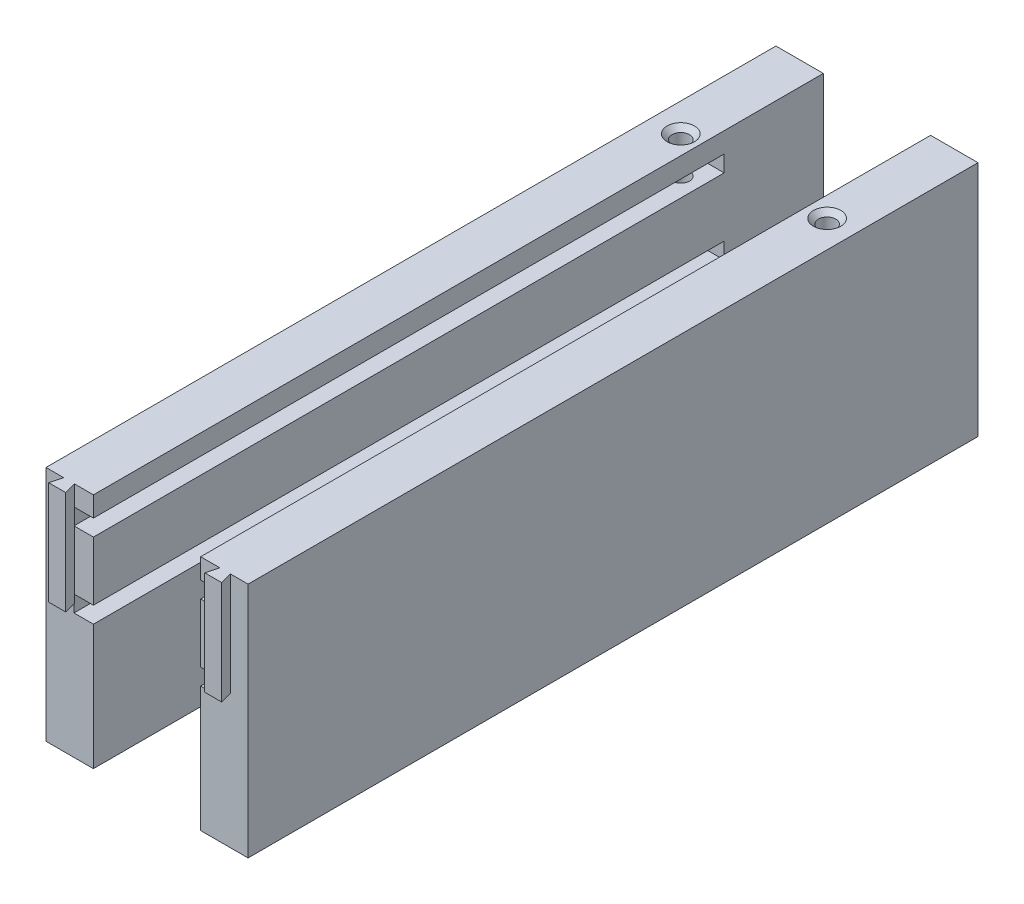
SolidWorks part; units mm, degrees
ref_plane "Front Plane" through (0, 0, 0) normal (0, 0, 1) x (1, 0, 0)
ref_plane "Top Plane" through (0, 0, 0) normal (0, 1, 0) x (1, 0, 0)
ref_plane "Right Plane" through (0, 0, 0) normal (1, 0, 0) x (0, 0, -1)
sketch "Sketch1" plane through (0, 0, 0) normal (1, 0, 0) x (0, 0, -1)
  line L1 (-64.8048, 14.1795) -> (82.1952, 14.1795)
  line L2 (-64.8048, 14.1795) -> (-64.8048, -32.8205)
  line L3 (-64.8048, -32.8205) -> (82.1952, -32.8205)
  line L4 (82.1952, 14.1795) -> (82.1952, -32.8205)
  dimension "D1" = 147
  dimension "D2" = 47
extrude "Boss-Extrude1" add sketch "Sketch1" along normal blind 8 contours L2 L3 L4 L1
sketch "Sketch12" plane through (0, 14.1795, 0) normal (0, 1, 0) x (1, 0, 0)
  line L0 (0, -62.4548) -> (2.1097, -62.4548)
  line L1 (0, -64.8048) -> (0, 82.1952) construction
  line L2 (2.1097, -62.4548) -> (1.48, -64.8048)
  line L3 (8, -64.8048) -> (0, -64.8048) construction
  line L4 (1.48, -64.8048) -> (0, -64.8048)
  line L5 (0, -64.8048) -> (0, -62.4548)
  line L6 (8, -62.4548) -> (8, -64.8048)
  line L7 (8, -64.8048) -> (8, 82.1952) construction
  line L8 (8, -64.8048) -> (4.8394, -64.8048)
  line L9 (4.8394, -64.8048) -> (4.2097, -62.4548)
  line L10 (4.2097, -62.4548) -> (8, -62.4548)
  dimension "D1" = 2.35
  dimension "D3" = 105
  dimension "D4" = 105
  dimension "D5" = 2.1
  dimension "D6" = 1.48
extrude "Cut-Extrude8" cut sketch "Sketch12" against normal blind 25
sketch "Sketch43" plane through (8, 0, 0) normal (1, 0, 0) x (0, 0, -1)
  line L0 (82.1952, -32.8205) -> (82.1952, -22.8205) construction
  line L2 (82.1952, -22.8205) -> (77.1952, -22.8205) construction
  line L3 (77.1952, -22.8205) -> (77.1952, -7.8205)
  line L4 (77.1952, -7.8205) -> (72.1952, -7.8205)
  line L5 (72.1952, -7.8205) -> (72.1952, -22.8205)
  line L6 (72.1952, -22.8205) -> (77.1952, -22.8205)
  dimension "D1" = 15
  dimension "D2" = 5
  dimension "D3" = 5
  dimension "D4" = 10
extrude "Boss-Extrude8" add sketch "Sketch43" along normal blind 6
sketch "Sketch44" plane through (8, 0, 0) normal (1, 0, 0) x (0, 0, -1)
  line L0 (82.1952, -32.8205) -> (67.1952, -32.8205) construction
  line L1 (-64.8048, -32.8205) -> (82.1952, -32.8205) construction
  line L2 (67.1952, -32.8205) -> (67.1952, -21.8205)
  line L3 (67.1952, -21.8205) -> (52.1952, -21.8205)
  line L4 (52.1952, -21.8205) -> (52.1952, -32.8205)
  line L5 (52.1952, -32.8205) -> (67.1952, -32.8205)
  dimension "D1" = 15
  dimension "D2" = 15
  dimension "D3" = 11
extrude "Boss-Extrude9" add sketch "Sketch44" along normal blind 6
sketch "Sketch13" plane through (0, -32.8205, 0) normal (0, -1, 0) x (1, 0, 0)
  line L1 (-1.916, 64.8048) -> (10.084, 64.8048)
  line L2 (-1.916, 64.8048) -> (-1.916, 62.4548)
  line L3 (-1.916, 62.4548) -> (10.084, 62.4548)
  line L4 (10.084, 64.8048) -> (10.084, 62.4548)
  line L7 (8, 64.8048) -> (0, 64.8048) construction
  dimension "D1" = 2.35
  dimension "D2" = 12
extrude "Cut-Extrude9" cut sketch "Sketch13" against normal blind 26.5
sketch "Sketch46" plane through (0, 0, 62.4548) normal (0, 0, 1) x (1, 0, 0)
  line L0 (8, 14.1795) -> (8, 10.1795) construction
  line L1 (8, -32.8205) -> (8, 14.1795) construction
  line L2 (8, 10.1795) -> (8, 6.9295)
  line L3 (8, 6.9295) -> (8, -4.7705) construction
  line L4 (8, -4.7705) -> (8, -8.0205)
  line L5 (8, 10.1795) -> (4.15, 10.1795)
  line L7 (4.15, 10.1795) -> (4.15, 6.9295)
  line L8 (4.15, 6.9295) -> (8, 6.9295)
  line L9 (8, -4.7705) -> (4.15, -4.7705)
  line L10 (4.15, -4.7705) -> (4.15, -8.0205)
  line L11 (4.15, -8.0205) -> (8, -8.0205)
  dimension "D1" = 4
  dimension "D2" = 3.25
  dimension "D3" = 11.7
  dimension "D4" = 3.25
  dimension "D5" = 3.85
  dimension "D6" = 3.85
extrude "Cut-Extrude15" cut sketch "Sketch46" against normal blind 125
ref_plane "Plane1" through (18.625, 0, 0) normal (-1, 0, 0) x (0, 0, 1)
sketch "Sketch47" plane through (0, 14.1795, 0) normal (0, 1, 0) x (1, 0, 0)
  line L0 (0, -62.4548) -> (-1.3972, -62.4548)
  line L1 (0, -62.4548) -> (0, 82.1952)
  line L2 (-1.3972, -62.4548) -> (-1.3972, 82.1952)
  line L3 (0, 82.1952) -> (-1.3972, 82.1952)
extrude "Boss-Extrude10" add sketch "Sketch47" against normal blind 47
mirror "Mirror4" about plane through (18.625, 0, 0) normal (-1, 0, 0) of bodies 140 113
hole_wizard "#8-32 Tapped Hole1" positions "Sketch35" profile "Sketch37" tap size "#8-32" standard "ANSI Inch"
sketch "Sketch35" plane through (0, 14.1795, 0) normal (0, 1, 0) x (1, 0, 0)
  point P0 (33.25, 57.6952)
  point P3 (4.25, 57.6952)
  point P4 (32.7599, 102.828)
  point P5 (33.25, 50.6952)
  point P7 (4.25, 50.6952)
sketch "Sketch37" plane through (33.25, 14.1795, -57.6952) normal (1, 0, 0) x (0, 0, 1)
  line L0 (0, 0) -> (0, 10.7074)
  line L1 (0, 10.7074) -> (1.7272, 9.6696)
  line L2 (1.7272, 9.6696) -> (1.7272, 0.9906)
  line L3 (1.7272, 0.9906) -> (2.7178, 0)
  line L5 (2.7178, 0) -> (0, 0)
  line L6 (-1.7272, 0.9906) -> (-2.7178, 0) construction
  line L10 (0, 10.7074) -> (-1.7272, 9.6696) construction
  line L11 (0, -6.35) -> (0, 107.95) construction
  dimension "Tap Drill Dia." = 3.4544
  dimension "Tap Drill Depth" = 10.7074
  dimension "Near C'Sink Dia." = 5.4356
  dimension "Near C'Sink Angle" = 90
  dimension "Drill Angle" = 118
cosmetic thread "Hole Thread2" parameters "D1"=8.33, "D2"=4.1656
cosmetic thread "Hole Thread6" parameters "D1"=8.33, "D2"=4.1656
thread "Thread3" pitch 0.7937 start angle 0, offset 1, length 10, pitch 0.7937, diameter 3.4544
ref_plane "Plane6" through (31.5228, 9.1889, -120.8538) normal (0, 0, 1) x (-1, 0, 0)
sketch "Thread Profile5" plane through (31.5228, 9.1889, -120.8538) normal (0, 0, 1) x (-1, 0, 0)
  line L0 (0, 0) -> (0, 0.7937) construction
  line L1 (0, 0) -> (0.4296, 0.248)
  line L2 (0.4296, 0.248) -> (0.4296, 0.3473)
  line L3 (0.4296, 0.3473) -> (0, 0.5953)
  line L4 (0.4296, 0.2977) -> (0, 0.2977) construction
  line L11 (0, 0) -> (0, 0.5953)
  point P2 (0, 0)
  dimension "Pitch" = 0.7937
  dimension "Profile_Angle" = 60
  dimension "Profile_Land" = 0.0992
  dimension "Profile_Height" = 0.4296
thread "Thread4" pitch 0.7937 start angle 0, offset 1, length 10, pitch 0.7937, diameter 3.4544
ref_plane "Plane7" through (2.2728, 9.1889, -120.8538) normal (0, 0, 1) x (-1, 0, 0)
sketch "Thread Profile6" plane through (2.2728, 9.1889, -120.8538) normal (0, 0, 1) x (-1, 0, 0)
  line L0 (0, 0) -> (0, 0.7937) construction
  line L1 (0, 0) -> (0.4296, 0.248)
  line L2 (0.4296, 0.248) -> (0.4296, 0.3473)
  line L3 (0.4296, 0.3473) -> (0, 0.5953)
  line L4 (0.4296, 0.2977) -> (0, 0.2977) construction
  line L11 (0, 0) -> (0, 0.5953)
  point P2 (0, 0)
  dimension "Pitch" = 0.7937
  dimension "Profile_Angle" = 60
  dimension "Profile_Land" = 0.0992
  dimension "Profile_Height" = 0.4296
